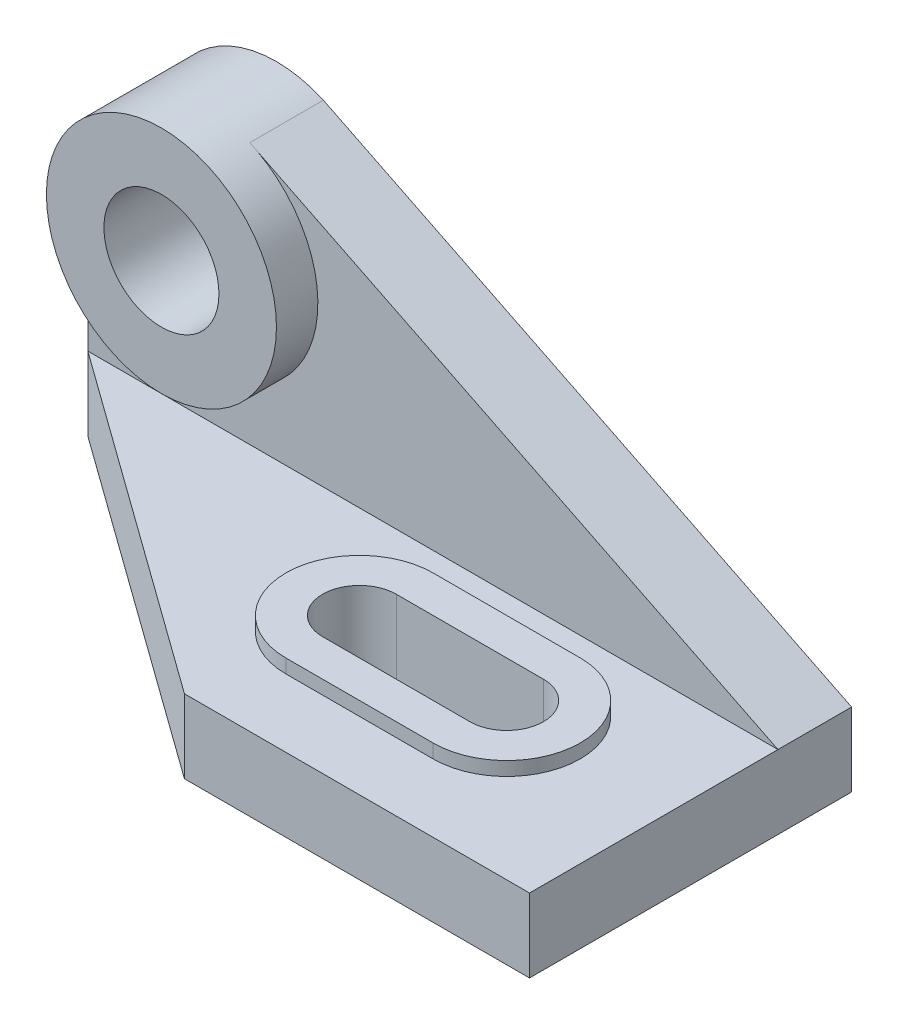
SolidWorks part; units mm, degrees
ref_plane "Front Plane" through (0, 0, 0) normal (0, 0, 1) x (1, 0, 0)
ref_plane "Top Plane" through (0, 0, 0) normal (0, 1, 0) x (1, 0, 0)
ref_plane "Right Plane" through (0, 0, 0) normal (1, 0, 0) x (0, 0, -1)
sketch "Sketch1" plane through (0, 0, 0) normal (0, 0, 1) x (1, 0, 0)
  line L0 (-66.557, 0) -> (83.443, 0)
  line L1 (-66.557, -16) -> (83.443, -16)
  line L2 (-66.557, 0) -> (-41.557, 0) construction
  line L3 (83.443, 0) -> (-31.3608, 56.8262)
  line L4 (-66.557, -16) -> (-66.557, 34)
  line L5 (83.443, 0) -> (83.443, -16)
  line L7 (-66.557, 34) -> (-41.557, 34) construction
  circle A2 centre (-41.557, 34) radius 25
  circle A3 centre (-41.557, 34) radius 12.5
  dimension "D1" = 16
extrude "Boss-Extrude4" add sketch "Sketch1" along normal blind 16 contours L3 A2 A3 | A2 L4 L0 L3 | L5 L0 L4 L1
sketch "Sketch6" plane through (0, 0, 16) normal (0, 0, 1) x (1, 0, 0)
  circle A0 centre (-41.557, 34) radius 12.5
  circle A1 centre (-41.557, 34) radius 25
extrude "Boss-Extrude5" add sketch "Sketch6" along normal blind 9
sketch "Sketch7" plane through (0, -16, 0) normal (0, -1, 0) x (1, 0, 0)
  line L0 (83.443, 16) -> (83.443, 70)
  line L1 (83.443, 70) -> (8.443, 70)
  line L2 (8.443, 70) -> (-66.557, 16)
  line L7 (-66.557, 0) -> (83.443, 0)
  line L8 (83.443, 0) -> (83.443, 16)
  line L9 (83.443, 16) -> (-66.557, 16)
  line L10 (-66.557, 16) -> (-66.557, 0)
  line L13 (83.443, 16) -> (-66.557, 16)
  dimension "D1" = 0
extrude "Boss-Extrude6" add sketch "Sketch7" against normal blind 16
sketch "Sketch8" plane through (0, 0, 0) normal (0, 1, 0) x (1, 0, 0)
  line L0 (83.443, -70) -> (83.443, -39.2416) construction
  line L1 (83.443, -16) -> (83.443, -70) construction
  line L2 (83.443, -39.2416) -> (47.7217, -39.2416) construction
  line L3 (47.7217, -39.2416) -> (15.7217, -39.2416) construction
  line L4 (47.7217, -47.2416) -> (15.7217, -47.2416)
  line L5 (47.7217, -31.2416) -> (15.7217, -31.2416)
  arc A0 (47.7217, -47.2416) -> (47.7217, -31.2416) centre (47.7217, -39.2416) ccw
  arc A1 (15.7217, -31.2416) -> (15.7217, -47.2416) centre (15.7217, -39.2416) ccw
  point P6 (31.7217, -39.2416)
extrude "Cut-Extrude2" cut sketch "Sketch8" against normal through all
sketch "Sketch9" plane through (0, 0, 0) normal (0, 1, 0) x (1, 0, 0)
  line L0 (47.7217, -39.2416) -> (15.7217, -39.2416) construction
  line L1 (47.7217, -55.2416) -> (15.7217, -55.2416)
  line L2 (47.7217, -23.2416) -> (15.7217, -23.2416)
  arc A0 (47.7217, -55.2416) -> (47.7217, -23.2416) centre (47.7217, -39.2416) ccw
  arc A1 (15.7217, -23.2416) -> (15.7217, -55.2416) centre (15.7217, -39.2416) ccw
  point P3 (31.7217, -39.2416)
extrude "Boss-Extrude7" add sketch "Sketch9" along normal blind 3
sketch "Sketch10" plane through (0, 0, 0) normal (0, 1, 0) x (1, 0, 0)
  line L0 (47.7217, -39.2416) -> (15.7217, -39.2416) construction
  line L1 (47.7217, -47.2416) -> (15.7217, -47.2416)
  line L2 (47.7217, -31.2416) -> (15.7217, -31.2416)
  arc A0 (47.7217, -47.2416) -> (47.7217, -31.2416) centre (47.7217, -39.2416) ccw
  arc A1 (15.7217, -31.2416) -> (15.7217, -47.2416) centre (15.7217, -39.2416) ccw
  point P3 (31.7217, -39.2416)
extrude "Cut-Extrude6" cut sketch "Sketch10" along normal through all
